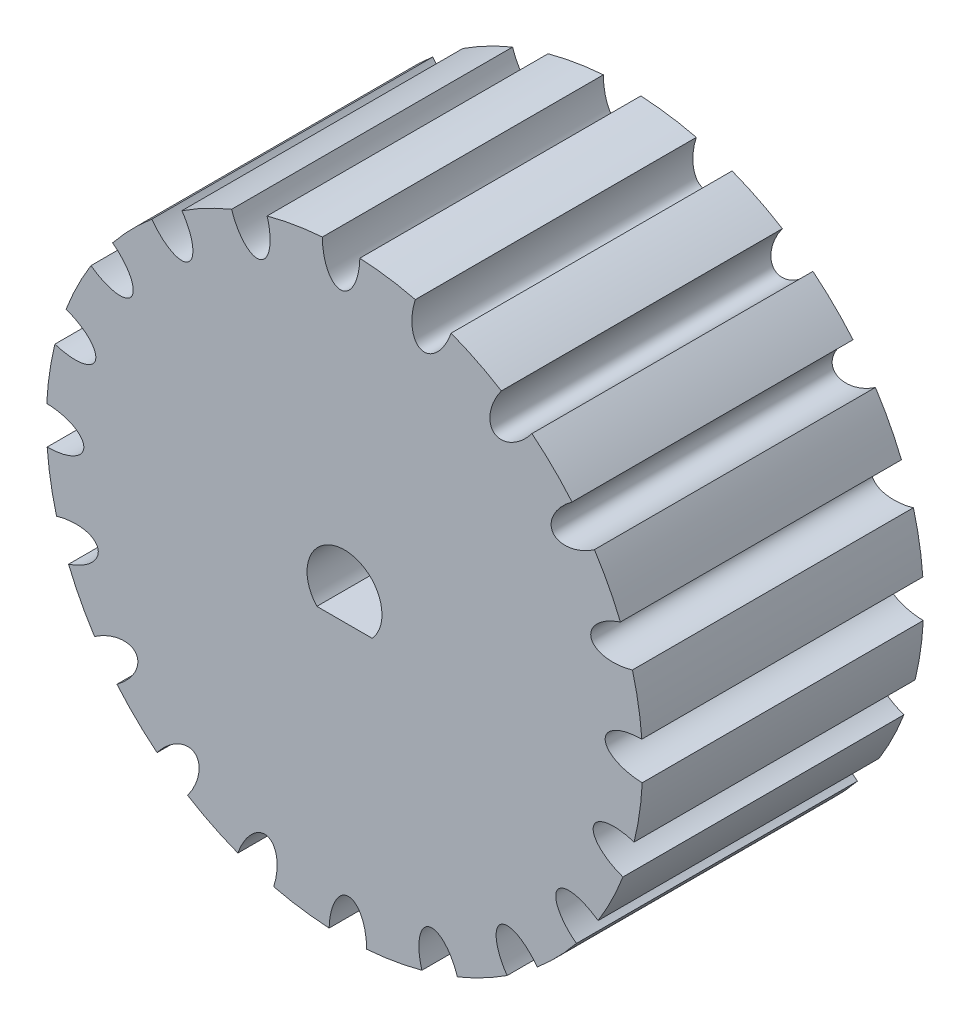
SolidWorks part; units mm, degrees
ref_plane "Спереди" through (0, 0, 0) normal (0, 0, 1) x (1, 0, 0)
ref_plane "Сверху" through (0, 0, 0) normal (0, 1, 0) x (1, 0, 0)
ref_plane "Справа" through (0, 0, 0) normal (1, 0, 0) x (0, 0, -1)
sketch "Эскиз1" plane through (0, 0, 0) normal (0, 0, 1) x (1, 0, 0)
  circle A0 centre (0, 0) radius 15.9155
  dimension "D1" = 31.831
extrude "Бобышка-Вытянуть1" add sketch "Эскиз1" along normal blind 15
sketch "Эскиз2" plane through (0, 0, 15) normal (0, 0, 1) x (1, 0, 0)
  line L0 (-1.4756, -1.35) -> (1.4756, -1.35)
  arc A0 (1.4756, -1.35) -> (-1.4756, -1.35) centre (0, 0) ccw
  dimension "D1" = 4
  dimension "D2" = 1.35
extrude "Вырез-Вытянуть1" cut sketch "Эскиз2" against normal blind 15
sketch "Эскиз3" plane through (0, 0, 15) normal (0, 0, 1) x (1, 0, 0)
  circle A0 centre (0, 0) radius 15.9155 construction
  ellipse E0 centre (12.7687, 9.5007) end of major axis (14.41, 10.6436) minor radius 1
  dimension "D1" = 2
  dimension "D2" = 1
extrude "Вырез-Вытянуть2" cut sketch "Эскиз3" against normal blind 15
pattern_circular "Круговой массив1" count 20 every 18 about axis through (0, 0, 15) along (0, 0, 1) of "Вырез-Вытянуть2"
